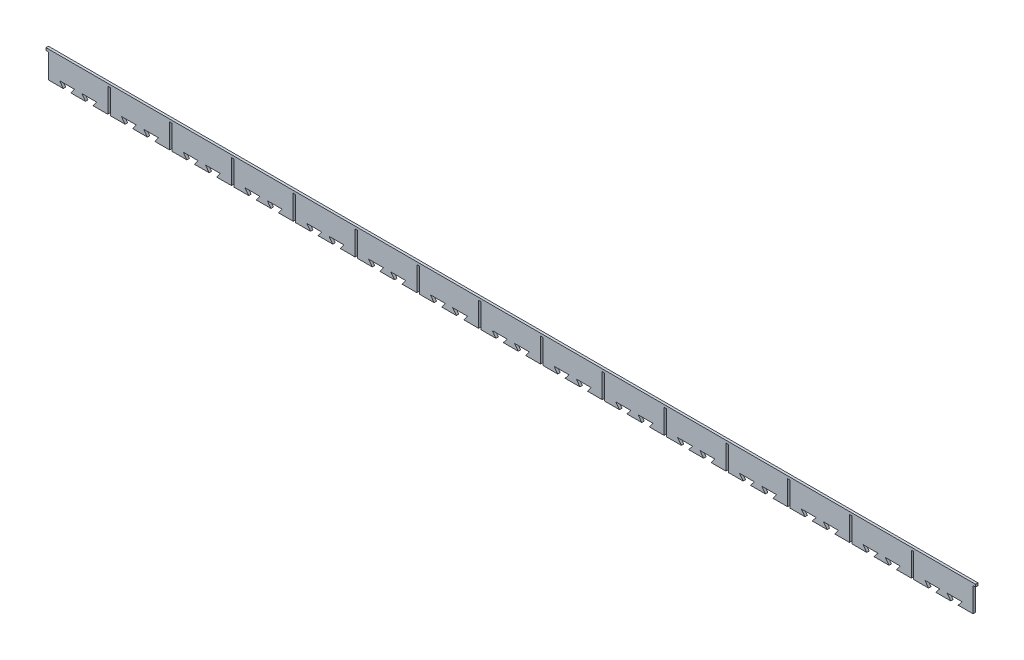
SolidWorks part; units mm, degrees
material "Cedar"
ref_plane "Front Plane" through (0, 0, 0) normal (0, 0, 1) x (1, 0, 0)
ref_plane "Top Plane" through (0, 0, 0) normal (0, 1, 0) x (1, 0, 0)
ref_plane "Right Plane" through (0, 0, 0) normal (1, 0, 0) x (0, 0, -1)
sketch "Sketch2" plane through (0, 0, 0) normal (0, 0, 1) x (1, 0, 0)
  line L0 (-778.4916, 45.21) -> (-778.4916, 41.21)
  line L1 (-778.4916, 41.21) -> (-774.4916, 41.21)
  line L2 (-774.4916, 41.21) -> (-774.4916, 1.805)
  line L3 (-774.4916, 1.805) -> (-750.4916, 1.805)
  line L4 (-756.4916, 9.805) -> (-732.4916, 9.805)
  line L5 (-750.4916, 1.805) -> (-756.4916, 9.805)
  line L6 (-738.4916, 1.805) -> (-714.4916, 1.805)
  line L7 (-738.4916, 1.805) -> (-732.4916, 9.805)
  line L8 (-578.4916, 41.21) -> (-574.4916, 41.21)
  line L9 (-714.4916, 1.805) -> (-720.4916, 9.805)
  line L10 (-720.4916, 9.805) -> (-696.4916, 9.805)
  line L11 (-702.4916, 1.805) -> (-696.4916, 9.805)
  line L12 (-702.4916, 1.805) -> (-678.4916, 1.805)
  line L13 (-778.4916, 45.21) -> (725.5084, 45.21)
  line L14 (-678.4916, 1.805) -> (-678.4916, 41.21)
  line L15 (-678.4916, 41.21) -> (-674.4916, 41.21)
  line L16 (-674.4916, 41.21) -> (-674.4916, 1.805)
  line L17 (-674.4916, 1.805) -> (-650.4916, 1.805)
  line L18 (-656.4916, 9.805) -> (-632.4916, 9.805)
  line L19 (-650.4916, 1.805) -> (-656.4916, 9.805)
  line L20 (-638.4916, 1.805) -> (-614.4916, 1.805)
  line L21 (-638.4916, 1.805) -> (-632.4916, 9.805)
  line L22 (-614.4916, 1.805) -> (-620.4916, 9.805)
  line L23 (-620.4916, 9.805) -> (-596.4916, 9.805)
  line L24 (-602.4916, 1.805) -> (-596.4916, 9.805)
  line L25 (-602.4916, 1.805) -> (-578.4916, 1.805)
  line L26 (-578.4916, 1.805) -> (-578.4916, 41.21)
  line L27 (-774.4916, 1.805) -> (855.8499, 1.805) construction
  line L28 (-574.4916, 41.21) -> (-574.4916, 1.805)
  line L29 (-574.4916, 1.805) -> (-550.4916, 1.805)
  line L30 (-556.4916, 9.805) -> (-532.4916, 9.805)
  line L31 (-550.4916, 1.805) -> (-556.4916, 9.805)
  line L32 (-538.4916, 1.805) -> (-514.4916, 1.805)
  line L33 (-538.4916, 1.805) -> (-532.4916, 9.805)
  line L34 (-514.4916, 1.805) -> (-520.4916, 9.805)
  line L35 (-520.4916, 9.805) -> (-496.4916, 9.805)
  line L36 (-502.4916, 1.805) -> (-496.4916, 9.805)
  line L37 (-502.4916, 1.805) -> (-478.4916, 1.805)
  line L38 (-478.4916, 1.805) -> (-478.4916, 41.21)
  line L39 (-478.4916, 41.21) -> (-474.4916, 41.21)
  line L40 (-474.4916, 41.21) -> (-474.4916, 1.805)
  line L41 (-474.4916, 1.805) -> (-450.4916, 1.805)
  line L42 (-456.4916, 9.805) -> (-432.4916, 9.805)
  line L43 (-450.4916, 1.805) -> (-456.4916, 9.805)
  line L44 (-438.4916, 1.805) -> (-414.4916, 1.805)
  line L45 (-438.4916, 1.805) -> (-432.4916, 9.805)
  line L46 (-414.4916, 1.805) -> (-420.4916, 9.805)
  line L47 (-420.4916, 9.805) -> (-396.4916, 9.805)
  line L48 (-402.4916, 1.805) -> (-396.4916, 9.805)
  line L49 (-402.4916, 1.805) -> (-378.4916, 1.805)
  line L50 (-378.4916, 1.805) -> (-378.4916, 41.21)
  line L51 (-378.4916, 41.21) -> (-374.4916, 41.21)
  line L52 (-374.4916, 41.21) -> (-374.4916, 1.805)
  line L53 (-374.4916, 1.805) -> (-350.4916, 1.805)
  line L54 (-356.4916, 9.805) -> (-332.4916, 9.805)
  line L55 (-350.4916, 1.805) -> (-356.4916, 9.805)
  line L56 (-338.4916, 1.805) -> (-314.4916, 1.805)
  line L57 (-338.4916, 1.805) -> (-332.4916, 9.805)
  line L58 (-314.4916, 1.805) -> (-320.4916, 9.805)
  line L59 (-320.4916, 9.805) -> (-296.4916, 9.805)
  line L60 (-302.4916, 1.805) -> (-296.4916, 9.805)
  line L61 (-302.4916, 1.805) -> (-278.4916, 1.805)
  line L62 (-278.4916, 1.805) -> (-278.4916, 41.21)
  line L63 (-278.4916, 41.21) -> (-274.4916, 41.21)
  line L64 (-274.4916, 41.21) -> (-274.4916, 1.805)
  line L65 (-274.4916, 1.805) -> (-250.4916, 1.805)
  line L66 (-256.4916, 9.805) -> (-232.4916, 9.805)
  line L67 (-250.4916, 1.805) -> (-256.4916, 9.805)
  line L68 (-238.4916, 1.805) -> (-214.4916, 1.805)
  line L69 (-238.4916, 1.805) -> (-232.4916, 9.805)
  line L70 (-214.4916, 1.805) -> (-220.4916, 9.805)
  line L71 (-220.4916, 9.805) -> (-196.4916, 9.805)
  line L72 (-202.4916, 1.805) -> (-196.4916, 9.805)
  line L73 (-202.4916, 1.805) -> (-178.4916, 1.805)
  line L74 (-178.4916, 1.805) -> (-178.4916, 41.21)
  line L75 (-178.4916, 41.21) -> (-174.4916, 41.21)
  line L76 (-174.4916, 41.21) -> (-174.4916, 1.805)
  line L77 (-174.4916, 1.805) -> (-150.4916, 1.805)
  line L78 (-156.4916, 9.805) -> (-132.4916, 9.805)
  line L79 (-150.4916, 1.805) -> (-156.4916, 9.805)
  line L80 (-138.4916, 1.805) -> (-114.4916, 1.805)
  line L81 (-138.4916, 1.805) -> (-132.4916, 9.805)
  line L82 (-114.4916, 1.805) -> (-120.4916, 9.805)
  line L83 (-120.4916, 9.805) -> (-96.4916, 9.805)
  line L84 (-102.4916, 1.805) -> (-96.4916, 9.805)
  line L85 (-102.4916, 1.805) -> (-78.4916, 1.805)
  line L86 (-78.4916, 1.805) -> (-78.4916, 41.21)
  line L87 (-78.4916, 41.21) -> (-74.4916, 41.21)
  line L88 (-74.4916, 41.21) -> (-74.4916, 1.805)
  line L89 (-74.4916, 1.805) -> (-50.4916, 1.805)
  line L90 (-56.4916, 9.805) -> (-32.4916, 9.805)
  line L91 (-50.4916, 1.805) -> (-56.4916, 9.805)
  line L92 (-38.4916, 1.805) -> (-14.4916, 1.805)
  line L93 (-38.4916, 1.805) -> (-32.4916, 9.805)
  line L94 (-14.4916, 1.805) -> (-20.4916, 9.805)
  line L95 (-20.4916, 9.805) -> (3.5084, 9.805)
  line L96 (-2.4916, 1.805) -> (3.5084, 9.805)
  line L97 (-2.4916, 1.805) -> (21.5084, 1.805)
  line L98 (21.5084, 1.805) -> (21.5084, 41.21)
  line L99 (21.5084, 41.21) -> (25.5084, 41.21)
  line L100 (25.5084, 41.21) -> (25.5084, 1.805)
  line L101 (25.5084, 1.805) -> (49.5084, 1.805)
  line L102 (43.5084, 9.805) -> (67.5084, 9.805)
  line L103 (49.5084, 1.805) -> (43.5084, 9.805)
  line L104 (61.5084, 1.805) -> (85.5084, 1.805)
  line L105 (61.5084, 1.805) -> (67.5084, 9.805)
  line L106 (85.5084, 1.805) -> (79.5084, 9.805)
  line L107 (79.5084, 9.805) -> (103.5084, 9.805)
  line L108 (97.5084, 1.805) -> (103.5084, 9.805)
  line L109 (97.5084, 1.805) -> (121.5084, 1.805)
  line L110 (121.5084, 1.805) -> (121.5084, 41.21)
  line L111 (121.5084, 41.21) -> (125.5084, 41.21)
  line L112 (125.5084, 41.21) -> (125.5084, 1.805)
  line L113 (125.5084, 1.805) -> (149.5084, 1.805)
  line L114 (143.5084, 9.805) -> (167.5084, 9.805)
  line L115 (149.5084, 1.805) -> (143.5084, 9.805)
  line L116 (161.5084, 1.805) -> (185.5084, 1.805)
  line L117 (161.5084, 1.805) -> (167.5084, 9.805)
  line L118 (185.5084, 1.805) -> (179.5084, 9.805)
  line L119 (179.5084, 9.805) -> (203.5084, 9.805)
  line L120 (197.5084, 1.805) -> (203.5084, 9.805)
  line L121 (197.5084, 1.805) -> (221.5084, 1.805)
  line L122 (221.5084, 1.805) -> (221.5084, 41.21)
  line L123 (221.5084, 41.21) -> (225.5084, 41.21)
  line L124 (225.5084, 41.21) -> (225.5084, 1.805)
  line L125 (225.5084, 1.805) -> (249.5084, 1.805)
  line L126 (243.5084, 9.805) -> (267.5084, 9.805)
  line L127 (249.5084, 1.805) -> (243.5084, 9.805)
  line L128 (261.5084, 1.805) -> (285.5084, 1.805)
  line L129 (261.5084, 1.805) -> (267.5084, 9.805)
  line L130 (285.5084, 1.805) -> (279.5084, 9.805)
  line L131 (279.5084, 9.805) -> (303.5084, 9.805)
  line L132 (297.5084, 1.805) -> (303.5084, 9.805)
  line L133 (297.5084, 1.805) -> (321.5084, 1.805)
  line L134 (321.5084, 1.805) -> (321.5084, 41.21)
  line L135 (321.5084, 41.21) -> (325.5084, 41.21)
  line L136 (325.5084, 41.21) -> (325.5084, 1.805)
  line L137 (325.5084, 1.805) -> (349.5084, 1.805)
  line L138 (343.5084, 9.805) -> (367.5084, 9.805)
  line L139 (349.5084, 1.805) -> (343.5084, 9.805)
  line L140 (361.5084, 1.805) -> (385.5084, 1.805)
  line L141 (361.5084, 1.805) -> (367.5084, 9.805)
  line L142 (385.5084, 1.805) -> (379.5084, 9.805)
  line L143 (379.5084, 9.805) -> (403.5084, 9.805)
  line L144 (397.5084, 1.805) -> (403.5084, 9.805)
  line L145 (397.5084, 1.805) -> (421.5084, 1.805)
  line L146 (421.5084, 1.805) -> (421.5084, 41.21)
  line L147 (421.5084, 41.21) -> (425.5084, 41.21)
  line L148 (425.5084, 41.21) -> (425.5084, 1.805)
  line L149 (425.5084, 1.805) -> (449.5084, 1.805)
  line L150 (443.5084, 9.805) -> (467.5084, 9.805)
  line L151 (449.5084, 1.805) -> (443.5084, 9.805)
  line L152 (461.5084, 1.805) -> (485.5084, 1.805)
  line L153 (461.5084, 1.805) -> (467.5084, 9.805)
  line L154 (485.5084, 1.805) -> (479.5084, 9.805)
  line L155 (479.5084, 9.805) -> (503.5084, 9.805)
  line L156 (497.5084, 1.805) -> (503.5084, 9.805)
  line L157 (497.5084, 1.805) -> (521.5084, 1.805)
  line L158 (521.5084, 1.805) -> (521.5084, 41.21)
  line L159 (521.5084, 41.21) -> (525.5084, 41.21)
  line L160 (525.5084, 41.21) -> (525.5084, 1.805)
  line L161 (525.5084, 1.805) -> (549.5084, 1.805)
  line L162 (543.5084, 9.805) -> (567.5084, 9.805)
  line L163 (549.5084, 1.805) -> (543.5084, 9.805)
  line L164 (561.5084, 1.805) -> (585.5084, 1.805)
  line L165 (561.5084, 1.805) -> (567.5084, 9.805)
  line L166 (585.5084, 1.805) -> (579.5084, 9.805)
  line L167 (579.5084, 9.805) -> (603.5084, 9.805)
  line L168 (597.5084, 1.805) -> (603.5084, 9.805)
  line L169 (597.5084, 1.805) -> (621.5084, 1.805)
  line L170 (621.5084, 1.805) -> (621.5084, 41.21)
  line L171 (621.5084, 41.21) -> (625.5084, 41.21)
  line L172 (625.5084, 41.21) -> (625.5084, 1.805)
  line L173 (625.5084, 1.805) -> (649.5084, 1.805)
  line L174 (643.5084, 9.805) -> (667.5084, 9.805)
  line L175 (649.5084, 1.805) -> (643.5084, 9.805)
  line L176 (661.5084, 1.805) -> (685.5084, 1.805)
  line L177 (661.5084, 1.805) -> (667.5084, 9.805)
  line L178 (685.5084, 1.805) -> (679.5084, 9.805)
  line L179 (679.5084, 9.805) -> (703.5084, 9.805)
  line L180 (697.5084, 1.805) -> (703.5084, 9.805)
  line L181 (697.5084, 1.805) -> (721.5084, 1.805)
  line L182 (721.5084, 1.805) -> (721.5084, 41.21)
  line L183 (725.5084, 45.21) -> (725.5084, 41.21)
  line L184 (725.5084, 41.21) -> (721.5084, 41.21)
  dimension "D2" = 4
  dimension "D3" = 4
  dimension "D4" = 1504
  dimension "D5" = 24
  dimension "D6" = 24
  dimension "D7" = 6
  dimension "D8" = 8
  dimension "D9" = 24
  dimension "D10" = 6
  dimension "D11" = 15
extrude "Boss-Extrude1" add sketch "Sketch2" along normal blind 4
